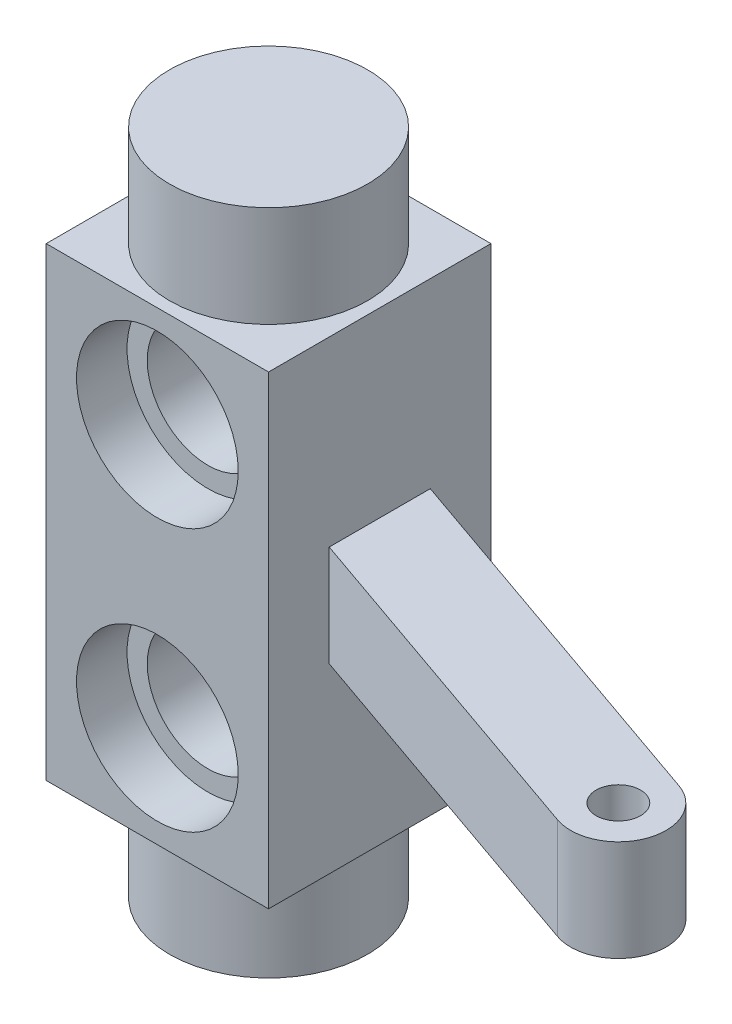
SolidWorks part; units mm, degrees
ref_plane "Front Plane" through (0, 0, 0) normal (0, 0, 1) x (1, 0, 0)
ref_plane "Top Plane" through (0, 0, 0) normal (0, 1, 0) x (1, 0, 0)
ref_plane "Right Plane" through (0, 0, 0) normal (1, 0, 0) x (0, 0, -1)
sketch "Sketch1" plane through (0, 0, 0) normal (0, 1, 0) x (1, 0, 0)
  circle A0 centre (0, 0) radius 4.9
  dimension "D1" = 9.8
extrude "Boss-Extrude1" add sketch "Sketch1" along normal blind 5
sketch "Sketch2" plane through (0, 5, 0) normal (0, 1, 0) x (1, 0, 0)
  line L1 (-5.5, -5.5) -> (5.5, -5.5)
  line L2 (-5.5, -5.5) -> (-5.5, 5.5)
  line L3 (-5.5, 5.5) -> (5.5, 5.5)
  line L4 (5.5, -5.5) -> (5.5, 5.5)
  line L5 (-5.5, -5.5) -> (5.5, 5.5) construction
  line L6 (-5.5, 5.5) -> (5.5, -5.5) construction
  point P0 (0, 0)
extrude "Boss-Extrude2" add sketch "Sketch2" along normal blind 23
sketch "Sketch3" plane through (0, 0, 5.5) normal (0, 0, 1) x (1, 0, 0)
  circle A0 centre (0, 10) radius 4
  dimension "D1" = 8
extrude "Cut-Extrude1" cut sketch "Sketch3" against normal blind 2.5
sketch "Sketch4" plane through (0, 0, -5.5) normal (0, 0, -1) x (-1, 0, 0)
  circle A0 centre (0, 10) radius 4
  dimension "D1" = 8
extrude "Cut-Extrude2" cut sketch "Sketch4" against normal blind 2.5
sketch "Sketch5" plane through (0, 0, -3) normal (0, 0, -1) x (-1, 0, 0)
  circle A0 centre (0, 10) radius 3
  dimension "D1" = 6
extrude "Cut-Extrude3" cut sketch "Sketch5" against normal up to next (6 mm away)
sketch "Sketch6" plane through (0, 28, 0) normal (0, 1, 0) x (1, 0, 0)
  circle A0 centre (0, 0) radius 4.9
  dimension "D1" = 9.8
extrude "Boss-Extrude3" add sketch "Sketch6" along normal blind 5
ref_plane "Plane1" through (0, 16.5, 0) normal (0, 1, 0) x (1, 0, 0)
sketch "Sketch7" plane through (0, 16.5, 0) normal (0, 1, 0) x (1, 0, 0)
  line L0 (5.5, 0) -> (5.5, 2.5)
  line L1 (5.5, -5.5) -> (5.5, 5.5) construction
  line L2 (5.5, 0) -> (5.5, -2.5)
  line L3 (5.5, 2.5) -> (5.5, -2.5)
  line L4 (5.5, 2.5) -> (24.3873, -4.078)
  line L5 (5.5, -2.5) -> (22.8343, -8.5371)
  arc A1 (22.8343, -8.5371) -> (24.3873, -4.078) centre (23.6108, -6.3076) ccw
  circle A2 centre (23.6108, -6.3076) radius 1.1
  point P4 (19.6655, -4.9335)
  dimension "D1" = 2.2
  dimension "D2" = 4.7218
extrude "Boss-Extrude4" add sketch "Sketch7" along normal mid plane 5 contours L5 A1 L4 L0 L2 A2
mirror "Mirror1" about plane through (0, 16.5, 0) normal (0, 1, 0) of "Cut-Extrude1"
mirror "Mirror2" about plane through (0, 16.5, 0) normal (0, 1, 0) of "Cut-Extrude2"
mirror "Mirror3" about plane through (0, 16.5, 0) normal (0, 1, 0) of "Cut-Extrude3"
